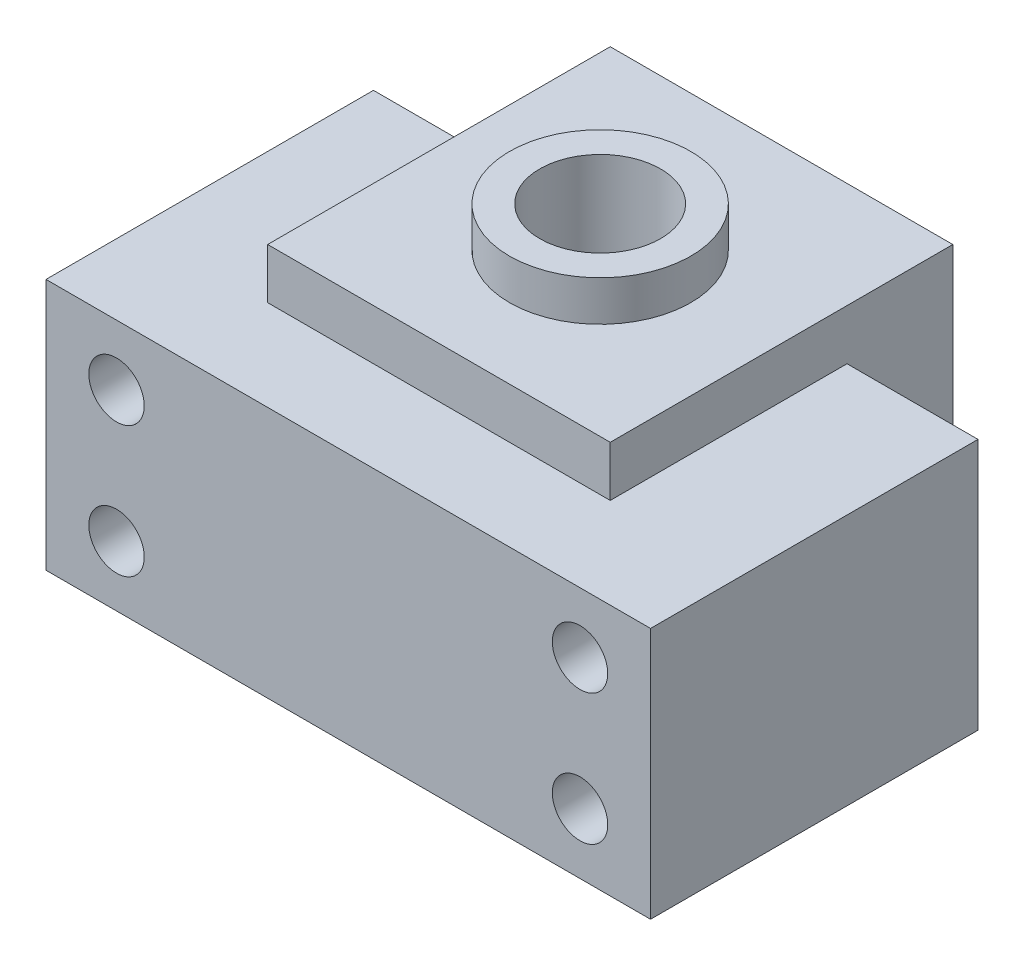
SolidWorks part; units mm, degrees
ref_plane "Front Plane" through (0, 0, 0) normal (0, 0, 1) x (1, 0, 0)
ref_plane "Top Plane" through (0, 0, 0) normal (0, 1, 0) x (1, 0, 0)
ref_plane "Right Plane" through (0, 0, 0) normal (1, 0, 0) x (0, 0, -1)
sketch "Sketch1" plane through (0, 0, 0) normal (0, 1, 0) x (1, 0, 0)
  line L1 (30, -21.5) -> (-30, -21.5)
  line L2 (30, -21.5) -> (30, 11)
  line L3 (17, 21.5) -> (-17, 21.5)
  line L4 (-30, -21.5) -> (-30, 11)
  line L5 (30, -21.5) -> (-17, 12.1833) construction
  line L6 (17, 12.1833) -> (-30, -21.5) construction
  line L9 (-30, 11) -> (-17, 11)
  line L10 (-17, 21.5) -> (-17, 11)
  line L15 (30, 11) -> (17, 11)
  line L16 (17, 21.5) -> (17, 11)
  circle A0 centre (0, 3.5) radius 6
  point P0 (0, 0)
  dimension "D5" = 12
  dimension "D1" = 60
  dimension "D2" = 10.5
  dimension "D3" = 34
  dimension "D4" = 43
  dimension "D6" = 25
extrude "Boss-Extrude1" add sketch "Sketch1" along normal blind 25
sketch "Sketch2" plane through (0, 0, -11) normal (0, 0, -1) x (-1, 0, 0)
  line L0 (-30, 0) -> (-17, 0) construction
  line L1 (0, 25) -> (0, 0) construction
  line L2 (-17, 25) -> (17, 25) construction
  circle A0 centre (-23, 19) radius 2.75
  circle A1 centre (-23, 6) radius 2.75
  circle A2 centre (23, 6) radius 2.75
  circle A3 centre (23, 19) radius 2.75
  dimension "D4" = 5.5
  dimension "D1" = 23
  dimension "D2" = 6
  dimension "D3" = 13
extrude "Cut-Extrude1" cut sketch "Sketch2" against normal through all
sketch "Sketch3" plane through (0, 25, 0) normal (0, 1, 0) x (1, 0, 0)
  line L0 (17, 11) -> (17, 21.5) construction
  line L1 (-17, 21.5) -> (17, 21.5)
  line L2 (-17, 21.5) -> (-17, -12.5)
  line L3 (-17, -12.5) -> (17, -12.5)
  line L4 (17, 21.5) -> (17, -12.5)
  circle A0 centre (0, 3.5) radius 6 construction
  circle A1 centre (0, 3.5) radius 6
extrude "Boss-Extrude2" add sketch "Sketch3" along normal blind 5
sketch "Sketch4" plane through (0, 30, 0) normal (0, 1, 0) x (1, 0, 0)
  circle A0 centre (0, 3.5) radius 9
  circle A1 centre (0, 3.5) radius 6 construction
  circle A2 centre (0, 3.5) radius 6
  dimension "D1" = 18
extrude "Boss-Extrude3" add sketch "Sketch4" along normal blind 4
